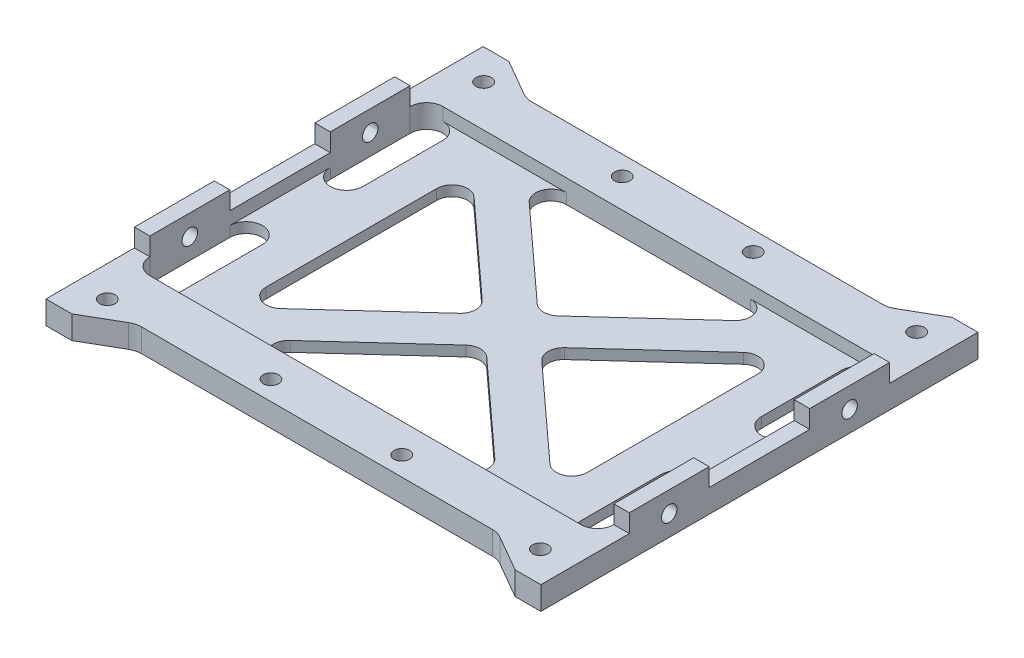
SolidWorks part; units mm, degrees
material "6061-T6 (SS)"
ref_plane "Front Plane" through (0, 0, 0) normal (0, 0, 1) x (1, 0, 0)
ref_plane "Top Plane" through (0, 0, 0) normal (0, 1, 0) x (1, 0, 0)
ref_plane "Right Plane" through (0, 0, 0) normal (1, 0, 0) x (0, 0, -1)
sketch "Sketch1" plane through (0, 0, 0) normal (0, 1, 0) x (1, 0, 0)
  line L0 (-41.825, 25.25) -> (-41.825, 9.75) construction
  line L1 (-48, -42.4) -> (-43, -42.4)
  line L2 (-48, -42.4) -> (-48, 42.4)
  line L3 (-48, 42.4) -> (-43, 42.4)
  line L4 (48, -42.4) -> (48, 42.4)
  line L5 (-48, -42.4) -> (48, 42.4) construction
  line L6 (-48, 42.4) -> (48, -42.4) construction
  line L7 (-38.65, 25.25) -> (-38.65, 9.75)
  line L8 (-45, 25.25) -> (-45, 9.75)
  line L9 (-41.825, -9.75) -> (-41.825, -25.25) construction
  line L10 (-38.65, -9.75) -> (-38.65, -25.25)
  line L11 (-45, -9.75) -> (-45, -25.25)
  line L12 (41.825, 25.25) -> (41.825, 9.75) construction
  line L13 (45, 25.25) -> (45, 9.75)
  line L14 (38.65, 25.25) -> (38.65, 9.75)
  line L15 (41.825, -9.75) -> (41.825, -25.25) construction
  line L16 (45, -9.75) -> (45, -25.25)
  line L17 (38.65, -9.75) -> (38.65, -25.25)
  line L18 (-43, -42.4) -> (-36.0093, -38.3639)
  line L19 (-34.0093, -37.828) -> (34.0093, -37.828)
  line L20 (36.0093, -38.3639) -> (43, -42.4)
  line L21 (43, 42.4) -> (36.0093, 38.3639)
  line L22 (34.0093, 37.828) -> (-34.0093, 37.828)
  line L23 (-36.0093, 38.3639) -> (-43, 42.4)
  line L24 (43, -42.4) -> (48, -42.4)
  line L25 (43, 42.4) -> (48, 42.4)
  line L26 (-38.5789, 34.078) -> (38.5789, 34.078) construction
  line L27 (38.5789, -34.078) -> (-38.5789, -34.078) construction
  line L29 (-42, 36.5) -> (42, 36.5) construction
  line L30 (-42, 36.5) -> (-42, -36.5) construction
  line L31 (-42, -36.5) -> (42, -36.5) construction
  line L32 (42, 36.5) -> (42, -36.5) construction
  line L33 (-42, 36.5) -> (42, -36.5) construction
  line L34 (-42, -36.5) -> (42, 36.5) construction
  arc A0 (-38.65, 25.25) -> (-45, 25.25) centre (-41.825, 25.25) ccw
  arc A1 (-45, 9.75) -> (-38.65, 9.75) centre (-41.825, 9.75) ccw
  arc A2 (-38.65, -9.75) -> (-45, -9.75) centre (-41.825, -9.75) ccw
  arc A3 (-45, -25.25) -> (-38.65, -25.25) centre (-41.825, -25.25) ccw
  arc A4 (45, 25.25) -> (38.65, 25.25) centre (41.825, 25.25) ccw
  arc A5 (38.65, 9.75) -> (45, 9.75) centre (41.825, 9.75) ccw
  arc A6 (45, -9.75) -> (38.65, -9.75) centre (41.825, -9.75) ccw
  arc A7 (38.65, -25.25) -> (45, -25.25) centre (41.825, -25.25) ccw
  arc A8 (36.0093, -38.3639) -> (34.0093, -37.828) centre (34.0093, -41.828) ccw
  arc A9 (-34.0093, -37.828) -> (-36.0093, -38.3639) centre (-34.0093, -41.828) ccw
  arc A10 (36.0093, 38.3639) -> (34.0093, 37.828) centre (34.0093, 41.828) cw
  arc A11 (-34.0093, 37.828) -> (-36.0093, 38.3639) centre (-34.0093, 41.828) cw
  circle A13 centre (-12.7, -34.078) radius 1.5
  circle A14 centre (12.7, -34.078) radius 1.5
  circle A17 centre (-12.7, 34.078) radius 1.5
  circle A18 centre (12.7, 34.078) radius 1.5
  circle A20 centre (-42, 36.5) radius 1.5
  circle A21 centre (42, 36.5) radius 1.5
  circle A22 centre (42, -36.5) radius 1.5
  circle A23 centre (-42, -36.5) radius 1.5
  point P0 (0, 0)
  point P8 (-41.825, 17.5)
  point P13 (-41.825, -17.5)
  point P20 (41.825, 17.5)
  point P27 (41.825, -17.5)
  point P44 (35.0811, -37.828)
  point P47 (-35.0811, -37.828)
  point P76 (0, 0)
  dimension "D3" = 3.175
  dimension "D15" = 4
  dimension "D31" = 3
  dimension "D21" = 3
  dimension "D1" = 96
  dimension "D2" = 84.8
  dimension "D4" = 35
  dimension "D5" = 24.9
  dimension "D6" = 35
  dimension "D7" = 24.9
  dimension "D8" = 15.5
  dimension "D9" = 3
  dimension "D10" = 3
  dimension "D11" = 4.572
  dimension "D13" = 30
  dimension "D14" = 30
  dimension "D17" = 30
  dimension "D18" = 30
  dimension "D19" = 4.572
  dimension "D20" = 3.75
  dimension "D22" = 25.4
  dimension "D23" = 12.7
  dimension "D26" = 25.4
  dimension "D27" = 12.7
  dimension "D12" = 5
  dimension "D16" = 5
  dimension "69" = 73
  dimension "D30" = 84
extrude "Boss-Extrude1" add sketch "Sketch1" along normal blind 2
sketch "Sketch2" plane through (0, 2, 0) normal (0, 1, 0) x (1, 0, 0)
  line L0 (38.65, -9.75) -> (38.65, -25.25) construction
  line L1 (38.65, 25.25) -> (38.65, 9.75) construction
  line L2 (-45, 25.25) -> (-45, 9.75) construction
  line L3 (-45, -9.75) -> (-45, -25.25) construction
  line L4 (38.65, -9.75) -> (38.65, -25.25)
  line L5 (38.65, 25.25) -> (38.65, 9.75)
  line L6 (-45, 25.25) -> (-45, 9.75)
  line L7 (-45, -9.75) -> (-45, -25.25)
  line L8 (-45, 9.75) -> (-45, -9.75)
  line L10 (-41.825, 28.425) -> (41.825, 28.425)
  line L13 (41.825, -28.425) -> (-41.825, -28.425)
  line L15 (45, 25.25) -> (45, -25.25)
  line L17 (-34.0093, -37.828) -> (34.0093, -37.828) construction
  line L18 (48, 42.4) -> (43, 42.4) construction
  line L19 (43, 42.4) -> (36.0093, 38.3639) construction
  line L20 (34.0093, 37.828) -> (-34.0093, 37.828) construction
  line L21 (-36.0093, 38.3639) -> (-43, 42.4) construction
  line L22 (-43, 42.4) -> (-48, 42.4) construction
  line L23 (-48, 42.4) -> (-48, -42.4) construction
  line L24 (-48, -42.4) -> (-43, -42.4) construction
  line L25 (-43, -42.4) -> (-36.0093, -38.3639) construction
  line L26 (48, -42.4) -> (48, 42.4) construction
  line L27 (43, -42.4) -> (48, -42.4) construction
  line L28 (36.0093, -38.3639) -> (43, -42.4) construction
  line L29 (48, 42.4) -> (43, 42.4)
  line L30 (43, 42.4) -> (36.0093, 38.3639)
  line L31 (34.0093, 37.828) -> (-34.0093, 37.828)
  line L32 (-36.0093, 38.3639) -> (-43, 42.4)
  line L33 (-43, 42.4) -> (-48, 42.4)
  line L34 (-48, 42.4) -> (-48, -42.4)
  line L35 (-48, -42.4) -> (-43, -42.4)
  line L36 (-43, -42.4) -> (-36.0093, -38.3639)
  line L37 (48, -42.4) -> (48, 42.4)
  line L38 (43, -42.4) -> (48, -42.4)
  line L39 (36.0093, -38.3639) -> (43, -42.4)
  line L40 (-34.0093, -37.828) -> (34.0093, -37.828)
  arc A0 (-45, -25.25) -> (-38.65, -25.25) centre (-41.825, -25.25) ccw construction
  arc A1 (38.65, -25.25) -> (45, -25.25) centre (41.825, -25.25) ccw construction
  arc A2 (45, 25.25) -> (38.65, 25.25) centre (41.825, 25.25) ccw construction
  arc A3 (-38.65, 25.25) -> (-45, 25.25) centre (-41.825, 25.25) ccw construction
  arc A4 (-45, -25.25) -> (-38.65, -25.25) centre (-41.825, -25.25) ccw
  arc A5 (38.65, -25.25) -> (45, -25.25) centre (41.825, -25.25) ccw
  arc A6 (45, 25.25) -> (38.65, 25.25) centre (41.825, 25.25) ccw
  arc A7 (-38.65, 25.25) -> (-45, 25.25) centre (-41.825, 25.25) ccw
  arc A8 (34.0093, 37.828) -> (36.0093, 38.3639) centre (34.0093, 41.828) ccw construction
  arc A9 (-36.0093, 38.3639) -> (-34.0093, 37.828) centre (-34.0093, 41.828) ccw construction
  arc A10 (36.0093, -38.3639) -> (34.0093, -37.828) centre (34.0093, -41.828) ccw construction
  arc A11 (34.0093, 37.828) -> (36.0093, 38.3639) centre (34.0093, 41.828) ccw
  arc A12 (-36.0093, 38.3639) -> (-34.0093, 37.828) centre (-34.0093, 41.828) ccw
  arc A13 (36.0093, -38.3639) -> (34.0093, -37.828) centre (34.0093, -41.828) ccw
  arc A14 (-34.0093, -37.828) -> (-36.0093, -38.3639) centre (-34.0093, -41.828) ccw construction
  arc A15 (-34.0093, -37.828) -> (-36.0093, -38.3639) centre (-34.0093, -41.828) ccw
  point P60 (0, 0)
extrude "Boss-Extrude2" add sketch "Sketch2" along normal blind 2.5
sketch "Sketch3" plane through (48, 0, 0) normal (1, 0, 0) x (0, 0, -1)
  line L0 (-42.4, 4.5) -> (42.4, 4.5) construction
  line L1 (-42.4, 4.5) -> (42.4, 4.5)
  line L3 (-25.25, 4.5) -> (-9.75, 4.5)
  line L4 (-25.25, 4.5) -> (-25.25, 8)
  line L5 (-25.25, 8) -> (-9.75, 8)
  line L6 (-9.75, 4.5) -> (-9.75, 8)
  line L7 (9.75, 4.5) -> (25.25, 4.5)
  line L8 (9.75, 4.5) -> (9.75, 8)
  line L9 (9.75, 8) -> (25.25, 8)
  line L10 (25.25, 4.5) -> (25.25, 8)
  line L18 (9.75, 0) -> (25.25, 0)
  line L19 (9.75, 2) -> (9.75, 0)
  line L20 (-9.75, 2) -> (9.75, 2)
  line L21 (-9.75, 0) -> (-9.75, 2)
  line L22 (-25.25, 0) -> (-9.75, 0)
  line L23 (-25.25, 4.5) -> (-25.25, 0)
  line L24 (25.25, 4.5) -> (-25.25, 4.5)
  line L25 (25.25, 0) -> (25.25, 4.5)
  line L26 (9.75, 0) -> (25.25, 0) construction
  line L27 (9.75, 2) -> (9.75, 0) construction
  line L28 (-9.75, 2) -> (9.75, 2) construction
  line L29 (-9.75, 0) -> (-9.75, 2) construction
  line L30 (-25.25, 0) -> (-9.75, 0) construction
  line L31 (-25.25, 4.5) -> (-25.25, 0) construction
  line L32 (25.25, 4.5) -> (-25.25, 4.5)
  line L33 (25.25, 0) -> (25.25, 4.5)
  dimension "D2" = 8
  dimension "D1" = 0
extrude "Boss-Extrude3" add sketch "Sketch3" against normal up to vertex (2.5 mm away) contours L1 L6 L5 L4 | L1 L10 L9 L8
sketch "Sketch4" plane through (48, 0, 0) normal (1, 0, 0) x (0, 0, -1)
  line L0 (-25.25, 8) -> (-25.25, 0) construction
  line L1 (-42.4, 0) -> (42.4, 0) construction
  line L2 (-25.25, 4) -> (17.5, 4) construction
  line L3 (-9.75, 4.5) -> (9.75, 4.5) construction
  line L4 (-17.5, 8) -> (-17.5, 0) construction
  line L5 (-25.25, 8) -> (-9.75, 8) construction
  line L7 (17.5, 8) -> (17.5, 0) construction
  line L8 (9.75, 8) -> (25.25, 8) construction
  circle A0 centre (-17.5, 4) radius 1.5
  circle A1 centre (17.5, 4) radius 1.5
  dimension "D1" = 3
extrude "Cut-Extrude1" cut sketch "Sketch4" against normal blind 5
mirror "Mirror1" about plane through (0, 0, 0) normal (1, 0, 0) of "Cut-Extrude1", "Boss-Extrude3"
sketch "Sketch5" plane through (0, 2, 0) normal (0, 1, 0) x (1, 0, 0)
  line L0 (-41.825, 28.425) -> (41.825, 28.425) construction
  line L1 (-31.15, -28.425) -> (31.15, -28.425) construction
  line L2 (-31.15, -28.425) -> (-31.15, 28.425) construction
  line L3 (-31.15, 28.425) -> (31.15, 28.425) construction
  line L4 (31.15, -28.425) -> (31.15, 28.425) construction
  line L5 (41.825, -28.425) -> (-41.825, -28.425) construction
  line L6 (-38.65, 9.75) -> (-38.65, 25.25) construction
  line L7 (38.65, 25.25) -> (38.65, 9.75) construction
  line L8 (-31.15, -28.425) -> (31.15, 28.425) construction
  line L9 (31.15, -28.425) -> (-31.15, 28.425) construction
  line L10 (-26.1278, -18.7655) -> (-7.9918, -2.216)
  line L11 (-7.9918, 2.216) -> (-26.1278, 18.7655)
  line L12 (-31.15, 16.5495) -> (-31.15, -16.5495)
  line L19 (19.8706, 23.209) -> (2.0222, 6.9219)
  line L20 (-2.0222, 6.9219) -> (-19.8706, 23.209)
  line L21 (-17.8484, 28.425) -> (17.8484, 28.425)
  line L22 (-19.8706, -23.209) -> (-2.0222, -6.9219)
  line L23 (2.0222, -6.9219) -> (19.8706, -23.209)
  line L24 (17.8484, -28.425) -> (-17.8484, -28.425)
  line L25 (7.9918, 2.216) -> (26.1278, 18.7655)
  line L26 (31.15, 16.5495) -> (31.15, -16.5495)
  line L27 (26.1278, -18.7655) -> (7.9918, -2.216)
  arc A0 (-19.8706, -23.209) -> (-17.8484, -28.425) centre (-17.8484, -25.425) ccw
  arc A1 (17.8484, -28.425) -> (19.8706, -23.209) centre (17.8484, -25.425) ccw
  arc A2 (31.15, -16.5495) -> (26.1278, -18.7655) centre (28.15, -16.5495) cw
  arc A3 (31.15, 16.5495) -> (26.1278, 18.7655) centre (28.15, 16.5495) ccw
  arc A4 (19.8706, 23.209) -> (17.8484, 28.425) centre (17.8484, 25.425) ccw
  arc A5 (-17.8484, 28.425) -> (-19.8706, 23.209) centre (-17.8484, 25.425) ccw
  arc A6 (-26.1278, 18.7655) -> (-31.15, 16.5495) centre (-28.15, 16.5495) ccw
  arc A7 (-31.15, -16.5495) -> (-26.1278, -18.7655) centre (-28.15, -16.5495) ccw
  arc A8 (-2.0222, -6.9219) -> (2.0222, -6.9219) centre (0, -9.1379) cw
  arc A9 (7.9918, -2.216) -> (7.9918, 2.216) centre (10.014, 0) cw
  arc A10 (2.0222, 6.9219) -> (-2.0222, 6.9219) centre (0, 9.1379) cw
  arc A11 (-7.9918, 2.216) -> (-7.9918, -2.216) centre (-10.014, 0) cw
  point P26 (-25.5867, -28.425)
  point P29 (25.5867, -28.425)
  point P32 (31.15, -23.3484)
  point P35 (31.15, 23.3484)
  point P38 (25.5867, 28.425)
  point P41 (-25.5867, 28.425)
  point P44 (-31.15, 23.3484)
  point P47 (-31.15, -23.3484)
  dimension "D5" = 3
  dimension "D1" = 7.5
  dimension "D2" = 7.5
  dimension "D3" = 7.5
  dimension "D4" = 7.5
extrude "Cut-Extrude2" cut sketch "Sketch5" against normal through all
sketch "Sketch6" plane through (-48, 0, 0) normal (-1, 0, 0) x (0, 0, 1)
  line L0 (-25.25, 4.5) -> (-21.75, 8)
  line L1 (-9.75, 8) -> (-25.25, 8) construction
  line L2 (-9.75, 4.5) -> (-13.25, 8)
  line L3 (-13.25, 8) -> (-9.75, 8)
  line L4 (-9.75, 8) -> (-9.75, 4.5)
  line L5 (-21.75, 8) -> (-25.25, 8)
  line L6 (-25.25, 8) -> (-25.25, 4.5)
  line L7 (9.75, 4.5) -> (9.75, 8)
  line L8 (9.75, 8) -> (13.25, 8)
  line L9 (25.25, 8) -> (9.75, 8) construction
  line L10 (13.25, 8) -> (9.75, 4.5)
  line L11 (25.25, 4.5) -> (25.25, 8)
  line L12 (25.25, 8) -> (21.75, 8)
  line L13 (21.75, 8) -> (25.25, 4.5)
  dimension "D1" = 45
extrude "Cut-Extrude3" [suppressed] cut sketch "Sketch6" against normal through all
chamfer "Chamfer1" [suppressed] distance 2.5 angle 45
sketch "Sketch7" plane through (0, 4.5, 0) normal (0, 1, 0) x (1, 0, 0)
  line L0 (-48, 42.4) -> (-48, 25.25) construction
  line L1 (-43, 42.4) -> (-48, 42.4) construction
  line L2 (-36.0093, 38.3639) -> (-43, 42.4) construction
  line L3 (-48, 42.4) -> (-48, 25.25)
  line L4 (-43, 42.4) -> (-48, 42.4)
  line L5 (-36.0093, 38.3639) -> (-43, 42.4)
  line L6 (-46.6095, 36.5) -> (-46.6095, 30.3844)
  line L7 (-48, -25.25) -> (-48, -42.4) construction
  line L8 (-48, -42.4) -> (-43, -42.4) construction
  line L9 (-43, -42.4) -> (-36.0093, -38.3639) construction
  line L10 (-48, -25.25) -> (-48, -42.4)
  line L11 (-48, -42.4) -> (-43, -42.4)
  line L12 (-43, -42.4) -> (-36.0093, -38.3639)
  line L13 (-46.6095, -36.5) -> (-46.6095, -30.3844)
  arc A0 (-39.6952, 40.492) -> (-46.6095, 36.5) centre (-42, 36.5) ccw
  arc A1 (-47.1562, 28.366) -> (-48, 25.25) centre (-41.825, 25.25) ccw
  arc A2 (-46.6095, 30.3844) -> (-47.1562, 28.366) centre (-50.6095, 30.3844) cw
  arc A3 (-46.6095, -36.5) -> (-39.6952, -40.492) centre (-42, -36.5) ccw
  arc A4 (-48, -25.25) -> (-47.1562, -28.366) centre (-41.825, -25.25) ccw
  arc A5 (-47.1562, -28.366) -> (-46.6095, -30.3844) centre (-50.6095, -30.3844) cw
  line M10 (-48, 42.4) -> (-48, 25.25)
  line M23 (-43, 42.4) -> (-48, 42.4)
  dimension "D1" = 4
  dimension "D2" = 4
extrude "Cut-Extrude4" [suppressed] cut sketch "Sketch7" against normal through all contours A5 A4 L10 L11 L12 A3 L13 | A2 L6 A0 L5 A1 M23 M10
mirror "Mirror2" [suppressed] about plane through (0, 0, 0) normal (1, 0, 0)
equation "\"D5@Sketch1\"=(\"D2@Sketch1\"-\"D4@Sketch1\")/2"
equation "\"D6@Sketch1\"=\"D4@Sketch1\""
equation "\"D7@Sketch1\"=\"D5@Sketch1\""
equation "\"D10@Sketch1\"=\"D9@Sketch1\""
equation "\"D19@Sketch1\"=\"D11@Sketch1\""
equation "\"D18@Sketch1\"=\"D17@Sketch1\""
equation "\"D13@Sketch1\"=\"D17@Sketch1\""
equation "\"D14@Sketch1\"=\"D17@Sketch1\""
equation "\"D23@Sketch1\"=\"D22@Sketch1\"/2"
equation "\"D26@Sketch1\"=\"D22@Sketch1\""
equation "\"D27@Sketch1\"=\"D23@Sketch1\""
equation "\"D2@Sketch5\"=\"D1@Sketch5\""
equation "\"D4@Sketch5\"=\"D3@Sketch5\""
